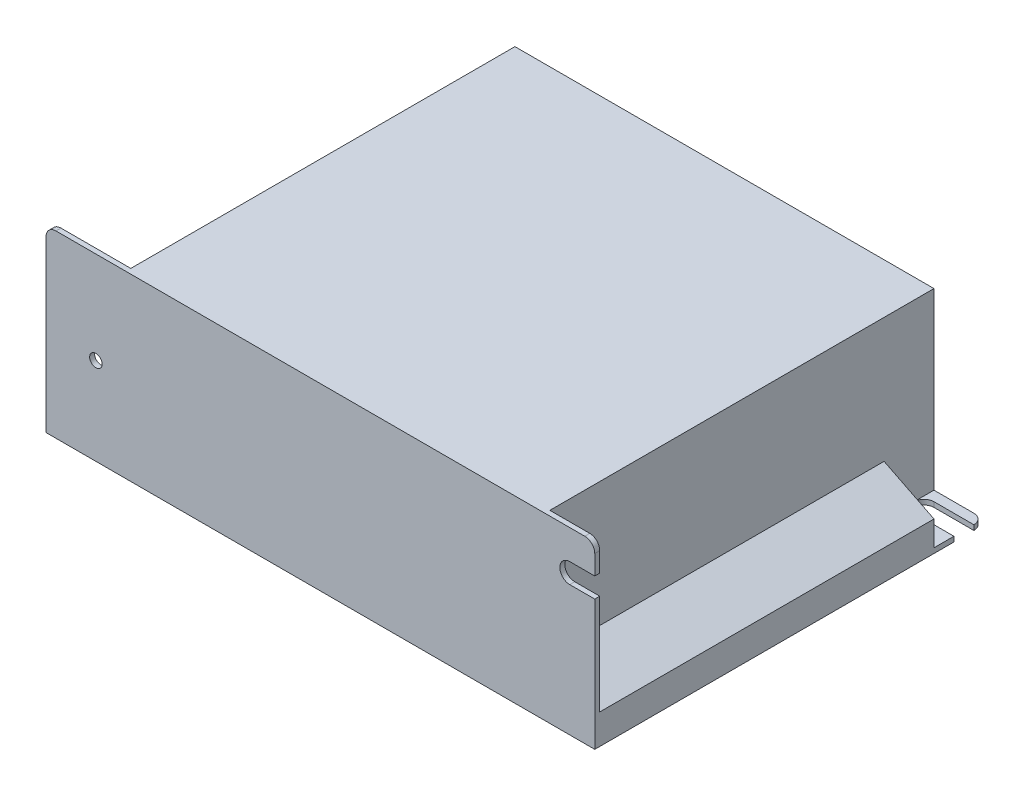
SolidWorks part; units mm, degrees
material "Aluminium"
ref_plane "Front Plane" through (0, 0, 0) normal (0, 0, 1) x (1, 0, 0)
ref_plane "Top Plane" through (0, 0, 0) normal (0, 1, 0) x (1, 0, 0)
ref_plane "Right Plane" through (0, 0, 0) normal (1, 0, 0) x (0, 0, -1)
sketch "Sketch1" plane through (0, 0, 0) normal (0, 1, 0) x (1, 0, 0)
  line L1 (0, 0) -> (110, 0)
  line L2 (0, 0) -> (0, 78)
  line L3 (0, 78) -> (110, 78)
  line L4 (110, 0) -> (110, 78)
  dimension "D1" = 78
  dimension "D2" = 110
extrude "Boss-Extrude1" add sketch "Sketch1" along normal blind 36
sketch "Sketch5" plane through (0, 0, 0) normal (0, -1, 0) x (-1, 0, 0)
  line L0 (-67.5, 0) -> (-67.5, 78) construction
  line L1 (0, 0) -> (-110, 0) construction
  line L2 (-110, 78) -> (0, 78) construction
  line L3 (-110, 0) -> (-110, 78) construction
  line L4 (-31.5, 0) -> (-31.5, 78) construction
  point P8 (-67.5, 25)
  point P9 (-67.5, 52.5)
  point P12 (-31.5, 52.5)
  dimension "D1" = 42.5
  dimension "D2" = 25
  dimension "D3" = 27.5
  dimension "D4" = 36
  dimension "D5" = 52.5
hole_wizard "M3 Tapped Hole2" positions "Sketch6" profile "Sketch7" tap size "M3" standard "ISO"
sketch "Sketch6" plane through (0, 0, 0) normal (0, -1, 0) x (-1, 0, 0)
  point P0 (-67.5, 25)
  point P3 (-67.5, 52.5)
  point P7 (-31.5, 52.5)
sketch "Sketch7" plane through (67.5, 0, -25) normal (1, 0, 0) x (0, 0, -1)
  line L0 (0, 0) -> (0, 5.7511)
  line L1 (0, 5.7511) -> (1.25, 5)
  line L2 (1.25, 5) -> (1.25, 0)
  line L5 (1.25, 0) -> (0, 0)
  line L10 (0, 5.7511) -> (-1.25, 5) construction
  line L11 (0, -6.35) -> (0, 107.95) construction
  dimension "Tap Drill Dia." = 2.5
  dimension "Tap Drill Depth" = 5
  dimension "Drill Angle" = 118
cosmetic thread "Hole Thread3" parameters "D1"=5, "D2"=3
cosmetic thread "Hole Thread4" parameters "D1"=5, "D2"=3
cosmetic thread "Hole Thread5" parameters "D1"=5, "D2"=3
sketch "Sketch8" plane through (0, 36, 0) normal (0, 1, 0) x (1, 0, 0)
  line L1 (0, 78) -> (16, 78)
  line L2 (0, 78) -> (0, 1)
  line L3 (0, 1) -> (16, 1)
  line L4 (16, 78) -> (16, 1)
  dimension "D1" = 16
  dimension "D2" = 77
extrude "Cut-Extrude2" cut sketch "Sketch8" against normal blind 35
sketch "Sketch9" plane through (0, 0, 0) normal (0, -1, 0) x (1, 0, 0)
  line L0 (5, 0) -> (5, -78) construction
  line L1 (0, 0) -> (110, 0) construction
  line L2 (110, -78) -> (0, -78) construction
  line L3 (0, -78) -> (0, 0) construction
  point P8 (5, -4)
  dimension "D1" = 5
  dimension "D2" = 4
hole_wizard "Ø3.0mm Dowel Hole1" positions "Sketch10" profile "Sketch11" hole size "Ø3.0" standard "ISO" end condition through all
sketch "Sketch10" plane through (0, 0, 0) normal (0, -1, 0) x (-1, 0, 0)
  point P0 (-5, 4)
sketch "Sketch11" plane through (5, 0, -4) normal (1, 0, 0) x (0, 0, -1)
  line L0 (0, 0) -> (0, 36)
  line L1 (0, 36) -> (1.5, 36)
  line L2 (1.5, 36) -> (1.5, 0)
  line L5 (1.5, 0) -> (0, 0)
  line L11 (0, -6.35) -> (0, 107.95) construction
  dimension "Thru Hole Dia." = 3
  dimension "Thru Hole Depth" = 36
sketch "Sketch12" plane through (0, 36, 0) normal (0, 1, 0) x (1, 0, 0)
  line L0 (110, 0) -> (110, 78) construction
  line L1 (110, 68) -> (100, 68)
  line L2 (110, 68) -> (110, 1)
  line L3 (110, 1) -> (100, 1)
  line L4 (100, 68) -> (100, 1)
  line L5 (110, 78) -> (16, 78) construction
  dimension "D1" = 67
  dimension "D2" = 10
  dimension "D3" = 10
extrude "Cut-Extrude4" cut sketch "Sketch12" against normal blind 25
sketch "Sketch13" plane through (0, 36, 0) normal (0, 1, 0) x (1, 0, 0)
  line L1 (110, 78) -> (100, 78)
  line L2 (110, 78) -> (110, 68)
  line L3 (110, 68) -> (100, 68)
  line L4 (100, 78) -> (100, 68)
extrude "Cut-Extrude5" cut sketch "Sketch13" against normal blind 35
sketch "Sketch15" plane through (0, 0, -68) normal (0, 0, -1) x (-1, 0, 0)
  line L0 (-110, 6) -> (-100, 11)
  line L1 (-110, 1) -> (-110, 11) construction
  line L2 (-100, 11) -> (-110, 11)
  line L3 (-110, 11) -> (-110, 6)
extrude "Cut-Extrude7" cut sketch "Sketch15" against normal blind 67
sketch "Sketch16" plane through (0, 0, -1) normal (0, 0, -1) x (-1, 0, 0)
  line L0 (-115, 28.0969) -> (-105, 28.0969) construction
  line L1 (-110, 6) -> (-110, 36) construction
  line L2 (-115, 30.0969) -> (-105, 30.0969)
  line L3 (-115, 26.0969) -> (-105, 26.0969)
  arc A0 (-115, 30.0969) -> (-115, 26.0969) centre (-115, 28.0969) ccw
  arc A1 (-105, 26.0969) -> (-105, 30.0969) centre (-105, 28.0969) ccw
  point P4 (-110, 28.0969)
  dimension "D2" = 5
  dimension "D1" = 4
extrude "Cut-Extrude8" cut sketch "Sketch16" against normal through all
hole_wizard "M3 Tapped Hole3" positions "Sketch18" profile "Sketch19" tap size "M3" standard "ISO" end condition through all
sketch "Sketch18" plane through (0, 0, 0) normal (0, 0, 1) x (1, 0, 0)
  line L0 (0, 36) -> (0, 0) construction
  line L1 (0, 36) -> (110, 36) construction
  point P0 (10, 17.5)
  dimension "D1" = 10
  dimension "D2" = 18.5
sketch "Sketch19" plane through (10, 17.5, 0) normal (1, 0, 0) x (0, -1, 0)
  line L0 (0, 0) -> (0, 78)
  line L1 (0, 78) -> (1.25, 78)
  line L2 (1.25, 78) -> (1.25, 0)
  line L5 (1.25, 0) -> (0, 0)
  line L11 (0, -6.35) -> (0, 107.95) construction
  dimension "Thru Tap Drill Dia." = 2.5
  dimension "Thru Tap Drill Depth" = 78
cosmetic thread "Hole Thread6" parameters "D2"=3
fillet "Fillet1" radius 2 4 edges at (0, 0.5, -78) (110, 0.5, -78) (110, 36, -0.5) (0, 36, -0.5)
sketch "Sketch20" plane through (0, 0, 0) normal (0, -1, 0) x (-1, 0, 0)
  line L0 (-102, 74) -> (-113.1364, 74) construction
  line L1 (-102, 72) -> (-113.1364, 72)
  line L2 (-102, 76) -> (-113.1364, 76)
  line L3 (-108, 78) -> (-2, 78) construction
  line L4 (-110, 0) -> (-110, 76) construction
  arc A0 (-102, 72) -> (-102, 76) centre (-102, 74) ccw
  arc A1 (-113.1364, 76) -> (-113.1364, 72) centre (-113.1364, 74) ccw
  point P2 (-107.5682, 74)
  dimension "D3" = 8
  dimension "D1" = 4
  dimension "D2" = 6
extrude "Cut-Extrude9" cut sketch "Sketch20" against normal through all
